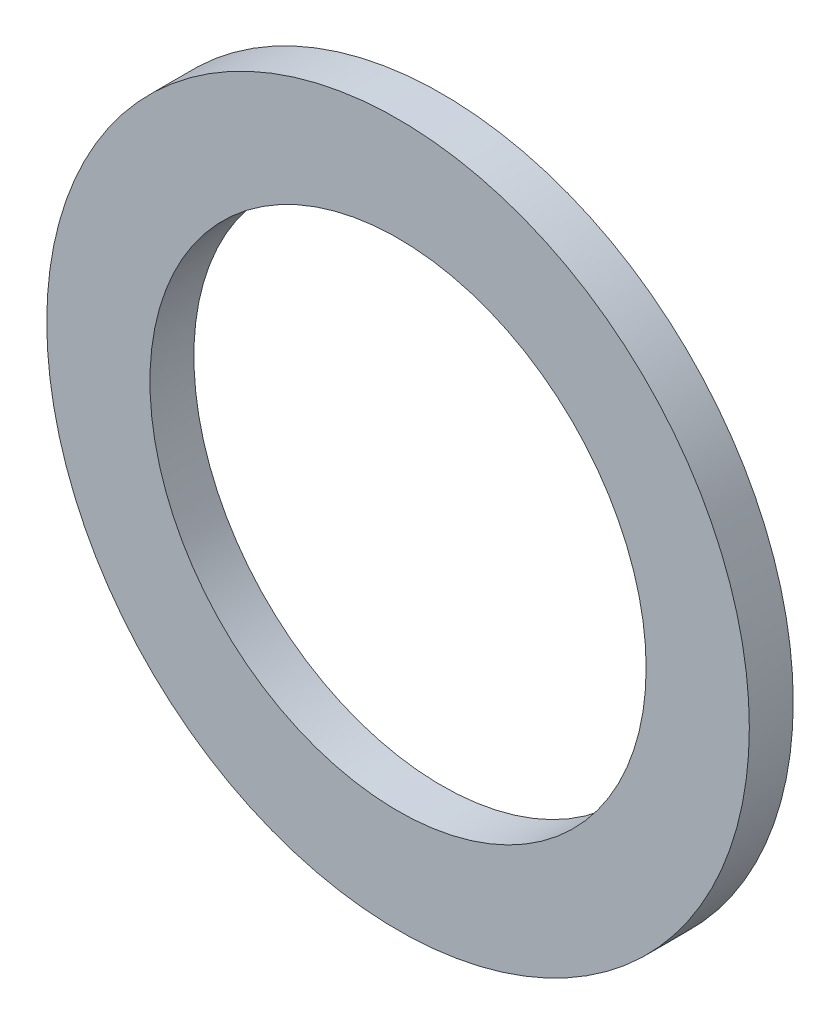
SolidWorks part; units mm, degrees
ref_plane "Front" through (0, 0, 0) normal (0, 0, 1) x (1, 0, 0)
ref_plane "Top" through (0, 0, 0) normal (0, 1, 0) x (1, 0, 0)
ref_plane "Right" through (0, 0, 0) normal (1, 0, 0) x (0, 0, -1)
sketch "Sketch1" plane through (0, 0, 0) normal (0, 0, 1) x (1, 0, 0)
  circle A0 centre (0, 0) radius 5.65
  circle A1 centre (0, 0) radius 8
  dimension "d1" = 11.3
  dimension "d2" = 16
extrude "Base-Extrude" add sketch "Sketch1" against normal blind 1
